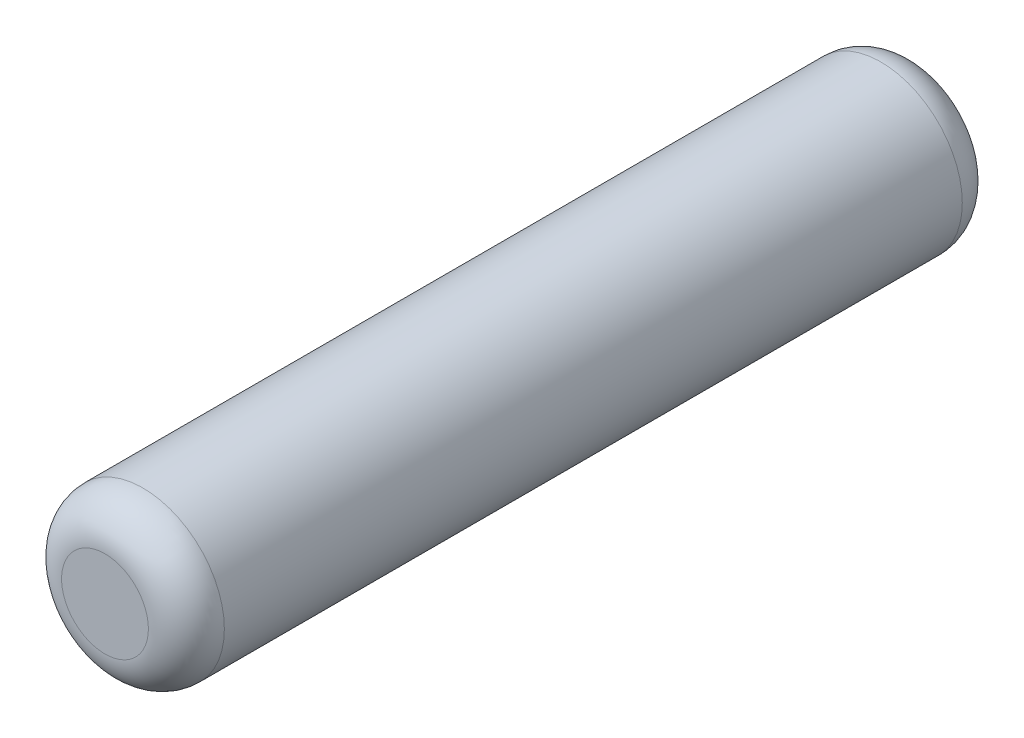
SolidWorks part; units mm, degrees
ref_plane "Front" through (0, 0, 0) normal (0, 0, 1) x (1, 0, 0)
ref_plane "Top" through (0, 0, 0) normal (0, 1, 0) x (1, 0, 0)
ref_plane "Right" through (0, 0, 0) normal (1, 0, 0) x (0, 0, -1)
sketch "Sketch1" plane through (0, 0, 0) normal (0, 0, 1) x (1, 0, 0)
  circle A0 centre (0, 0) radius 0.75
  dimension "D1" = 1.5
extrude "Boss-Extrude1" add sketch "Sketch1" along normal mid plane 7.5
fillet "Fillet1" radius 0.35 2 edges at (0.75, 0, -3.75) (0.75, 0, 3.75)
